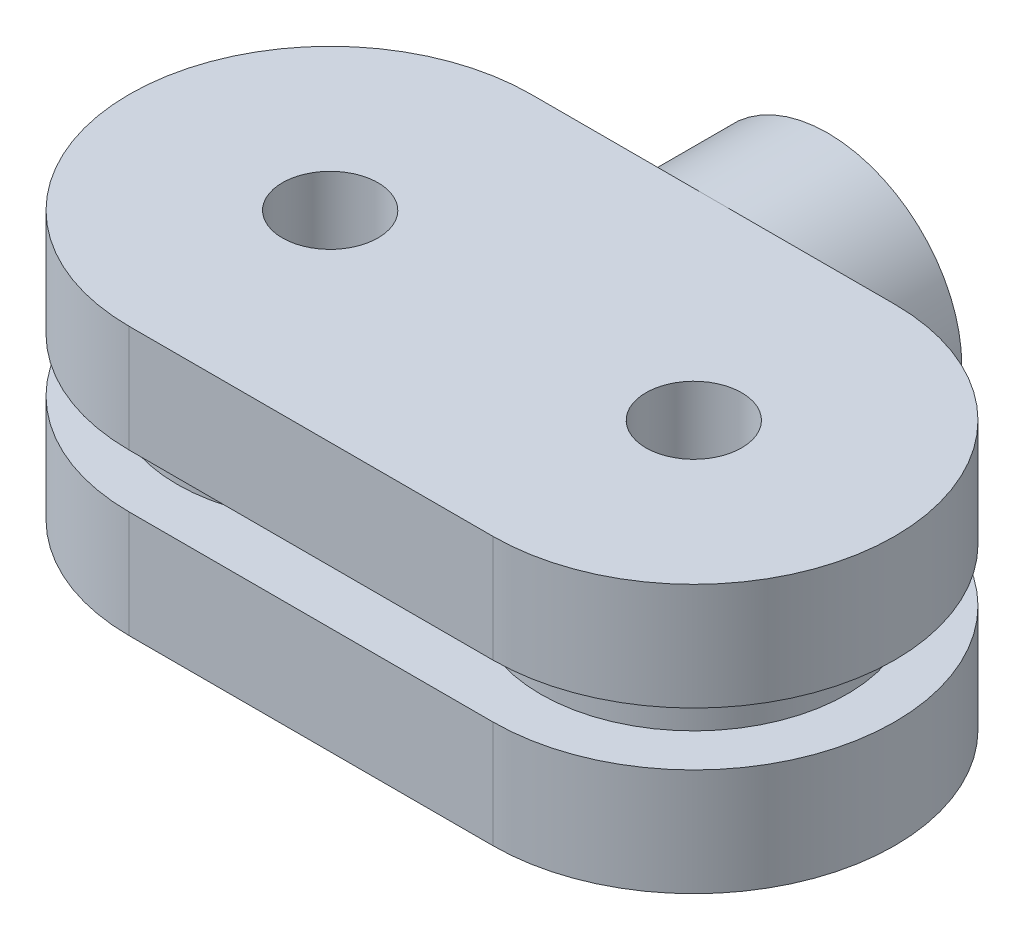
SolidWorks part; units mm, degrees
ref_plane "前视基准面" through (0, 0, 0) normal (0, 0, 1) x (1, 0, 0)
ref_plane "上视基准面" through (0, 0, 0) normal (0, 1, 0) x (1, 0, 0)
ref_plane "右视基准面" through (0, 0, 0) normal (1, 0, 0) x (0, 0, -1)
sketch "草图1" plane through (0, 0, 0) normal (0, 1, 0) x (1, 0, 0)
  line L0 (0, 0) -> (9.5, 0) construction
  line L1 (0, 5.25) -> (9.5, 5.25)
  line L2 (0, -5.25) -> (9.5, -5.25)
  arc A0 (0, 5.25) -> (0, -5.25) centre (0, 0) ccw
  arc A1 (9.5, -5.25) -> (9.5, 5.25) centre (9.5, 0) ccw
  circle A2 centre (0, 0) radius 1.25
  circle A3 centre (9.5, 0) radius 1.25
  point P3 (4.75, 0)
extrude "凸台-拉伸1" add sketch "草图1" along normal blind 2.8
sketch "草图2" plane through (0, 2.8, 0) normal (0, 1, 0) x (1, 0, 0)
  circle A0 centre (0, 0) radius 1.25
  circle A1 centre (0, 0) radius 4
  circle A2 centre (9.5, 0) radius 4
  circle A3 centre (9.5, 0) radius 1.25
extrude "凸台-拉伸2" add sketch "草图2" along normal blind 1.4
sketch "草图3" plane through (0, 4.2, 0) normal (0, 1, 0) x (1, 0, 0)
  line L0 (0, 0) -> (9.5, 0) construction
  line L1 (0, 5.25) -> (9.5, 5.25)
  line L2 (0, -5.25) -> (9.5, -5.25)
  arc A0 (0, 5.25) -> (0, -5.25) centre (0, 0) ccw
  arc A1 (9.5, -5.25) -> (9.5, 5.25) centre (9.5, 0) ccw
  circle A3 centre (0, 0) radius 1.25
  circle A4 centre (9.5, 0) radius 1.25
  point P4 (4.75, 0)
extrude "凸台-拉伸3" add sketch "草图3" along normal blind 2.8
sketch "草图4" plane through (0, 0, -5.25) normal (0, 0, -1) x (-1, 0, 0)
  line L0 (-9.5, 7) -> (0, 0)
  line L1 (0, 0) -> (0, 7)
  line L2 (0, 7) -> (-9.5, 0)
  circle A0 centre (-4.75, 3.5) radius 3.5
  circle A1 centre (-4.75, 3.5) radius 2
  line M5 (0, 2.8) -> (-9.5, 2.8)
extrude "凸台-拉伸4" add sketch "草图4" along normal blind 3 contours A1 L2 A0 L0 | A1 L0 A0 M5 | A1 A0 L2 M5 | A1 L2 A0 L0 | A1 A0 L2 M5 | A1 L0 A0 M5
sketch "草图5" plane through (0, 0, 5.25) normal (0, 0, 1) x (1, 0, 0)
  line L0 (4, 4.2) -> (5.5, 2.8)
  line L1 (0, 2.8) -> (9.5, 2.8) construction
  line L2 (5.5, 4.2) -> (5.5, 2.8) construction
  line L3 (5.5, 2.8) -> (5.5, 4.2)
  line L4 (5.5, 4.2) -> (13.5, 4.2) construction
  line L5 (5.5, 4.2) -> (4, 2.8)
  line L6 (4, 2.8) -> (4, 4.2) construction
  point P7 (4.75, 3.5)
sketch "草图6" plane through (0, 0, 5.25) normal (0, 0, 1) x (1, 0, 0)
  line L0 (4.75, 4.5) -> (4.75, 2.5)
  circle A0 centre (4.75, 3.5) radius 1
ref_plane "基准面1" through (4.75, 3.5, 5.25) normal (0, -1, 0) x (-1, 0, 0)
